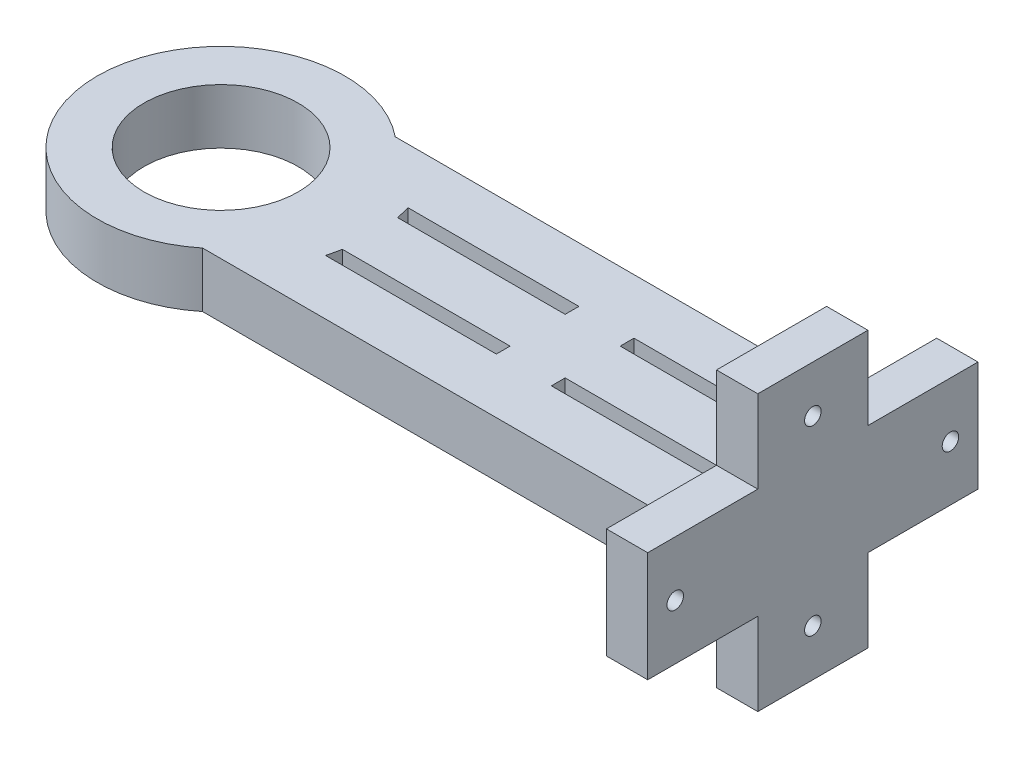
SolidWorks part; units mm, degrees
ref_plane "Front Plane" through (0, 0, 0) normal (0, 0, 1) x (1, 0, 0)
ref_plane "Top Plane" through (0, 0, 0) normal (0, 1, 0) x (1, 0, 0)
ref_plane "Right Plane" through (0, 0, 0) normal (1, 0, 0) x (0, 0, -1)
sketch "Sketch1" plane through (0, 0, 0) normal (0, 1, 0) x (1, 0, 0)
  line L1 (200, 15) -> (200, 10)
  line L2 (54.0833, 10) -> (200, 10)
  line L3 (52.915, 15) -> (200, 15)
  line L5 (-45, 0) -> (215, 0)
  line L6 (215, 60) -> (215, 0)
  line L7 (28.2843, 35) -> (200, 35)
  line L12 (200, 35) -> (200, 60)
  line L13 (200, 60) -> (215, 60)
  arc A1 (52.915, 15) -> (54.0833, 10) centre (0, 0) cw
  arc A4 (28.2843, 35) -> (-45, 0) centre (0, 0) ccw
  dimension "D1" = 10
  dimension "D7" = 55
  dimension "D5" = 45
  dimension "D2" = 215
  dimension "D3" = 20
  dimension "D4" = 15
  dimension "D6" = 5
  dimension "D8" = 60
extrude "Boss-Extrude1" add sketch "Sketch1" along normal blind 20
mirror "Mirror2" about plane through (-45, 20, 0) normal (0, 0, -1) of "Boss-Extrude1"
sketch "Sketch3" plane through (0, 20, 0) normal (0, 1, 0) x (1, 0, 0)
  circle A3 centre (0, 0) radius 28
  dimension "D1" = 28
extrude "Cut-Extrude2" cut sketch "Sketch3" against normal through all
sketch "Sketch5" plane through (0, 0, 0) normal (0, -1, 0) x (1, 0, 0)
  line L0 (215, 60) -> (200, 60) construction
  line L1 (200, 60) -> (215, 60)
  line L2 (200, 60) -> (200, -60)
  line L3 (200, -60) -> (215, -60)
  line L4 (215, 60) -> (215, -60)
  line L5 (200, -60) -> (200, -35) construction
extrude "Boss-Extrude3" add sketch "Sketch5" along normal blind 10
sketch "Sketch6" plane through (0, -10, 0) normal (0, -1, 0) x (1, 0, 0)
  line L0 (215, -60) -> (215, 60) construction
  line L1 (200, 20) -> (215, 20)
  line L2 (200, 20) -> (200, -20)
  line L3 (200, -20) -> (215, -20)
  line L4 (215, 20) -> (215, -20)
  line L5 (200, 20) -> (215, -20) construction
  line L6 (200, -20) -> (215, 20) construction
  line L7 (200, 60) -> (200, -60) construction
  point P0 (207.5, 0)
  dimension "D1" = 20
extrude "Boss-Extrude4" add sketch "Sketch6" along normal blind 30
sketch "Sketch10" plane through (200, 0, 0) normal (-1, 0, 0) x (0, 0, 1)
  line L1 (10, 0) -> (-10, 0) construction
  circle A0 centre (0, -23) radius 7.5
  point P14 (0, 0)
  dimension "D6" = 15
  dimension "D3" = 23
ref_plane "Plane3" through (0, 10, 0) normal (0, -1, 0) x (-1, 0, 0)
mirror "Mirror5" about plane through (0, 10, 0) normal (0, -1, 0) of "Boss-Extrude3"
mirror "Mirror6" about plane through (0, 10, 0) normal (0, -1, 0) of "Boss-Extrude4"
extrude "Cut-Extrude8" cut sketch "Sketch10" against normal blind 2
sketch "Sketch11" plane through (202, 0, 0) normal (-1, 0, 0) x (0, 0, 1)
  circle A0 centre (0, -23) radius 3
  circle A1 centre (0, -23) radius 7.5 construction
  dimension "D1" = 6
extrude "Cut-Extrude9" cut sketch "Sketch11" against normal through all
sketch "Sketch12" plane through (200, 0, 0) normal (-1, 0, 0) x (0, 0, 1)
  line L0 (-66, 10) -> (66, 10) construction
  line L1 (-35, 20) -> (-35, 0) construction
  circle A0 centre (-50, 10) radius 7.5
  dimension "D2" = 15
  dimension "D1" = 15
extrude "Cut-Extrude10" cut sketch "Sketch12" against normal blind 2
sketch "Sketch13" plane through (202, 0, 0) normal (-1, 0, 0) x (0, 0, 1)
  circle A0 centre (-50, 10) radius 3
  circle A1 centre (-50, 10) radius 7.5 construction
  dimension "D1" = 6
extrude "Cut-Extrude11" cut sketch "Sketch13" against normal through all
mirror "Mirror7" about plane through (0, 0, 0) normal (0, 0, 1) of "Cut-Extrude11", "Cut-Extrude10"
mirror "Mirror8" about plane through (0, 10, 0) normal (0, -1, 0) of "Cut-Extrude9", "Cut-Extrude8"
sketch "Sketch14" plane through (0, 20, 0) normal (0, 1, 0) x (1, 0, 0)
  line L0 (200, 15) -> (52.915, 15) construction
  line L1 (115, 15) -> (135, 15)
  line L2 (115, 15) -> (115, 10)
  line L3 (115, 10) -> (135, 10)
  line L4 (135, 15) -> (135, 10)
  line L5 (54.0833, 10) -> (200, 10) construction
  line L6 (200, -10) -> (200, 10) construction
  point P8 (135, 12.5)
  dimension "D1" = 20
  dimension "D2" = 65
extrude "Boss-Extrude5" add sketch "Sketch14" against normal blind 20
mirror "Mirror9" about plane through (0, 0, 0) normal (0, 0, 1) of "Boss-Extrude5"
ref_plane "Plane4" through (200, 0, 0) normal (-1, 0, 0) x (0, 0, 1)
split "Split1" trim tools "Plane4" bodies to split 130 resulting bodies 131 132
split "Split2" trim tools "Plane4" bodies to split 132 131 resulting bodies 133 134
